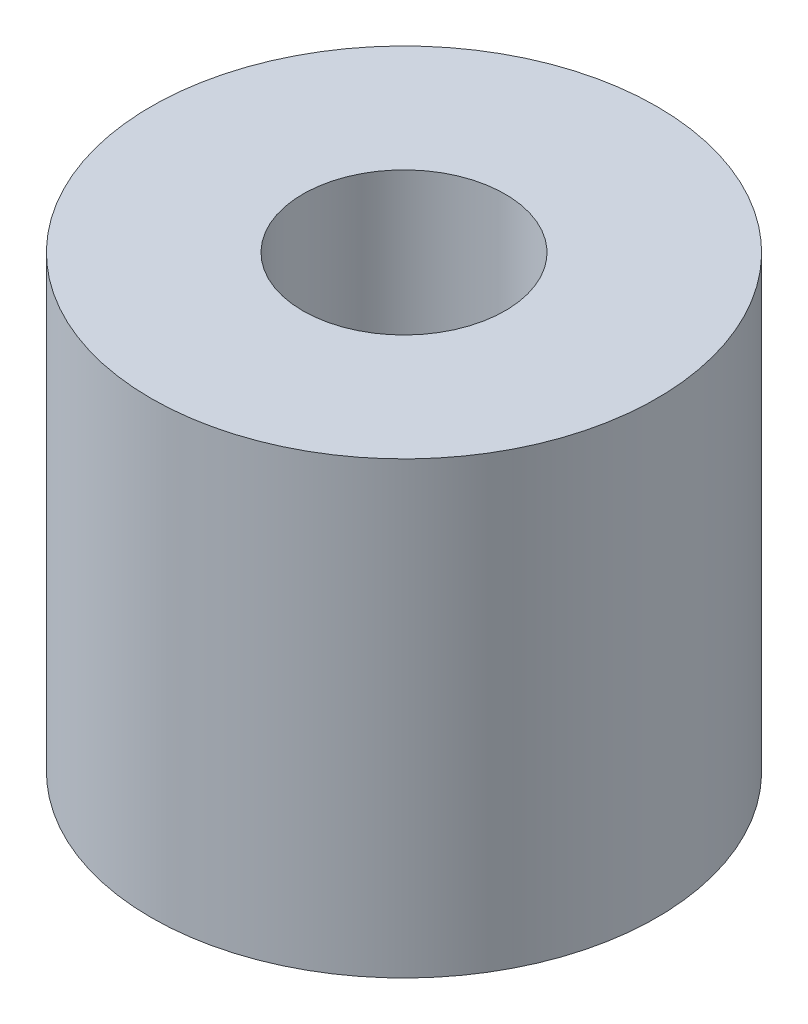
SolidWorks part; units mm, degrees
ref_plane "Alzado" through (0, 0, 0) normal (0, 0, 1) x (1, 0, 0)
ref_plane "Planta" through (0, 0, 0) normal (0, 1, 0) x (1, 0, 0)
ref_plane "Vista lateral" through (0, 0, 0) normal (1, 0, 0) x (0, 0, -1)
sketch "Croquis1" plane through (0, 0, 0) normal (0, 1, 0) x (1, 0, 0)
  circle A0 centre (0, 0) radius 4.5
  circle A1 centre (0, 0) radius 1.8
  dimension "D1" = 9
  dimension "D2" = 3.6
extrude "Saliente-Extruir1" add sketch "Croquis1" along normal blind 8
